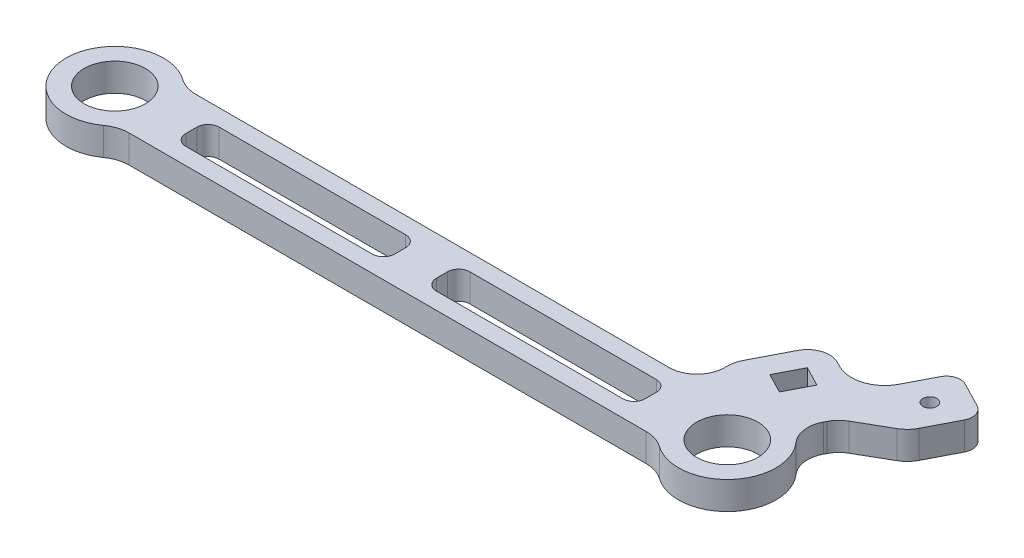
SolidWorks part; units mm, degrees
ref_plane "Front Plane" through (0, 0, 0) normal (0, 0, 1) x (1, 0, 0)
ref_plane "Top Plane" through (0, 0, 0) normal (0, 1, 0) x (1, 0, 0)
ref_plane "Right Plane" through (0, 0, 0) normal (1, 0, 0) x (0, 0, -1)
sketch "Sketch1" plane through (0, 0, 0) normal (0, 1, 0) x (1, 0, 0)
  line L0 (-36.9974, 0) -> (35.0826, 0) construction
  line L1 (12.7377, 12) -> (207.2623, 12)
  line L2 (12.7377, -12) -> (207.2623, -12)
  line L3 (110, 12) -> (110, -12) construction
  line L4 (27.5, 6) -> (102.5, 6)
  line L5 (27.5, 6) -> (27.5, -6)
  line L6 (27.5, -6) -> (102.5, -6)
  line L7 (102.5, 6) -> (102.5, -6)
  line L8 (27.5, 6) -> (102.5, -6) construction
  line L9 (27.5, -6) -> (102.5, 6) construction
  line L10 (192.5, -6) -> (117.5, 6) construction
  line L11 (192.5, 6) -> (117.5, -6) construction
  line L12 (117.5, 6) -> (117.5, -6)
  line L13 (192.5, -6) -> (117.5, -6)
  line L14 (192.5, 6) -> (192.5, -6)
  line L15 (192.5, 6) -> (117.5, 6)
  line L16 (220, 0) -> (256.3474, 70.3916) construction
  line L17 (249.5347, 35.4022) -> (233.5347, 26.2118)
  line L18 (245.3796, 60.0489) -> (254.265, 55.4609)
  line L19 (256.4137, 48.7242) -> (235.4745, 8.1726)
  line L20 (211.9804, 36.7789) -> (207.3924, 27.8935)
  line L21 (207.3924, 27.8935) -> (214.5007, 24.2231)
  line L22 (214.5007, 24.2231) -> (219.0887, 33.1085)
  line L23 (219.0887, 33.1085) -> (211.9804, 36.7789)
  line L24 (207.3924, 27.8935) -> (219.0887, 33.1085) construction
  line L25 (211.9804, 36.7789) -> (214.5007, 24.2231) construction
  line L26 (213.2406, 30.501) -> (236.0165, 18.7404) construction
  line L27 (204.8721, 40.4493) -> (197.0725, 25.3442)
  line L28 (197.0725, 25.3442) -> (197.0725, 12)
  line L29 (215.6509, 43.8872) -> (217.428, 42.9696)
  line L30 (233.5961, 48.1264) -> (238.6429, 57.9003)
  line L31 (233.5347, 26.2118) -> (228.0291, 15.5494)
  circle A0 centre (0, 0) radius 17.5
  circle A1 centre (220, 0) radius 17.5
  circle A2 centre (220, 0) radius 11
  circle A3 centre (0, 0) radius 11
  circle A4 centre (244.7755, 47.981) radius 2.5
  arc A5 (215.6509, 43.8872) -> (204.8721, 40.4493) centre (211.9804, 36.7789) ccw
  arc A6 (233.5961, 48.1264) -> (217.428, 42.9696) centre (222.9336, 53.632) cw
  arc A7 (256.4137, 48.7242) -> (254.265, 55.4609) centre (251.971, 51.0182) ccw
  arc A8 (238.6429, 57.9003) -> (245.3796, 60.0489) centre (243.0856, 55.6063) cw
  point P13 (65, 0)
  point P24 (155, 0)
  point P44 (208.5426, 47.5576)
  dimension "D2" = 22
  dimension "D3" = 35
  dimension "D12" = 5
  dimension "D20" = 8
  dimension "D22" = 12
  dimension "D23" = 5
  dimension "D1" = 220
  dimension "D4" = 12
  dimension "D5" = 12
  dimension "D6" = 75
  dimension "D7" = 45
  dimension "D8" = 117.31
  dimension "D9" = 10
  dimension "D10" = 54
  dimension "D11" = 65
  dimension "D13" = 10
  dimension "D14" = 8
  dimension "D15" = 30
  dimension "D16" = 16
  dimension "D17" = 8
  dimension "D18" = 8
  dimension "D19" = 25
  dimension "D21" = 10
  dimension "D24" = 12
  dimension "D25" = 16
extrude "Boss-Extrude1" add sketch "Sketch1" along normal blind 10 contours A1 L1 A0 L2 L4 L7 L6 L5 L15 L14 L13 L12 | A0 A3 | A1 A2 | A8 L30 A6 L29 A5 L27 L28 L1 A1 L19 A7 L18 A4 L23 L22 L21 L20
fillet "Fillet1" radius 4 8 edges at (102.5, 5, -6) (192.5, 5, 6) (192.5, 5, -6) (117.5, 5, 6) (117.5, 5, -6) (27.5, 5, 6) (27.5, 5, -6) (102.5, 5, 6)
fillet "Fillet2" radius 12 3 edges at (207.2623, 5, 12) (12.7377, 5, -12) (12.7377, 5, 12)
fillet "Fillet3" radius 10 5 edges at (197.0725, 5, -12) (197.0725, 5, -25.3442) (228.0291, 5, -15.5494) (233.5347, 5, -26.2118) (249.5347, 5, -35.4022)
